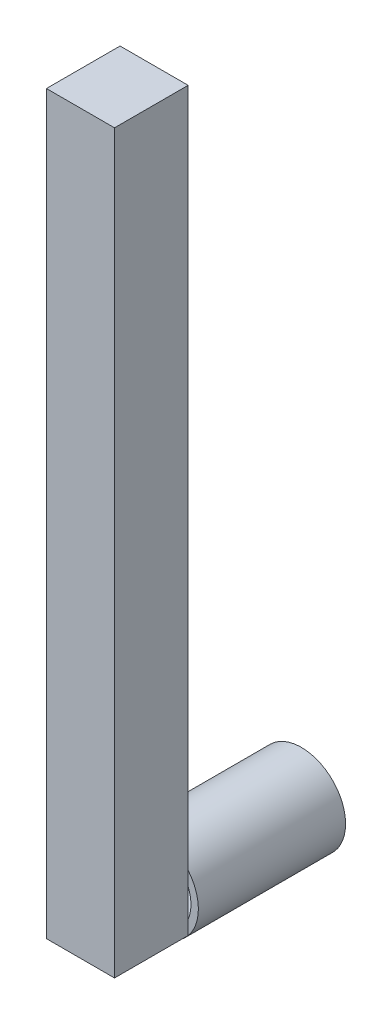
SolidWorks part; units mm, degrees
ref_plane "Alzado" through (0, 0, 0) normal (0, 0, 1) x (1, 0, 0)
ref_plane "Planta" through (0, 0, 0) normal (0, 1, 0) x (1, 0, 0)
ref_plane "Vista lateral" through (0, 0, 0) normal (1, 0, 0) x (0, 0, -1)
sketch "Croquis1" plane through (0, 0, 0) normal (0, 0, 1) x (1, 0, 0)
  circle A0 centre (0, 0) radius 2.5
  circle A1 centre (0, 0) radius 3
  dimension "D1" = 5
  dimension "D2" = 6
extrude "Saliente-Extruir1" add sketch "Croquis1" along normal blind 10
sketch "Croquis2" plane through (0, 0, 10) normal (0, 0, 1) x (1, 0, 0)
  line L5 (-2.3135, -1.9099) -> (2.3095, -1.9099)
  line L6 (-2.3135, -1.9099) -> (-2.3135, 48.0901)
  line L7 (-2.3135, 48.0901) -> (2.3095, 48.0901)
  line L8 (2.3095, -1.9099) -> (2.3095, 48.0901)
  circle A1 centre (0, 0) radius 3 construction
  dimension "D1" = 50
extrude "Saliente-Extruir2" add sketch "Croquis2" along normal blind 5
